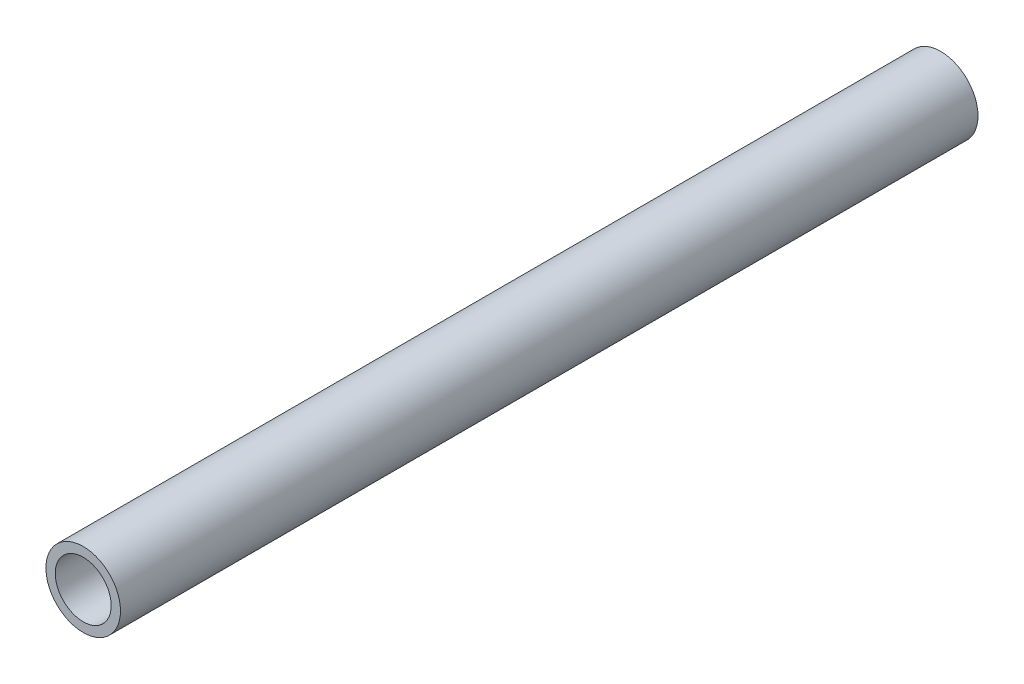
SolidWorks part; units mm, degrees
ref_plane "Front Plane" through (0, 0, 0) normal (0, 0, 1) x (1, 0, 0)
ref_plane "Top Plane" through (0, 0, 0) normal (0, 1, 0) x (1, 0, 0)
ref_plane "Right Plane" through (0, 0, 0) normal (1, 0, 0) x (0, 0, -1)
sketch "Sketch1" plane through (0, 0, 0) normal (0, 0, 1) x (1, 0, 0)
  circle A0 centre (0, 0) radius 12.7
  circle A1 centre (0, 0) radius 9.525
  dimension "D1" = 25.4
  dimension "D2" = 19.05
extrude "Boss-Extrude1" add sketch "Sketch1" along normal blind 292.1
